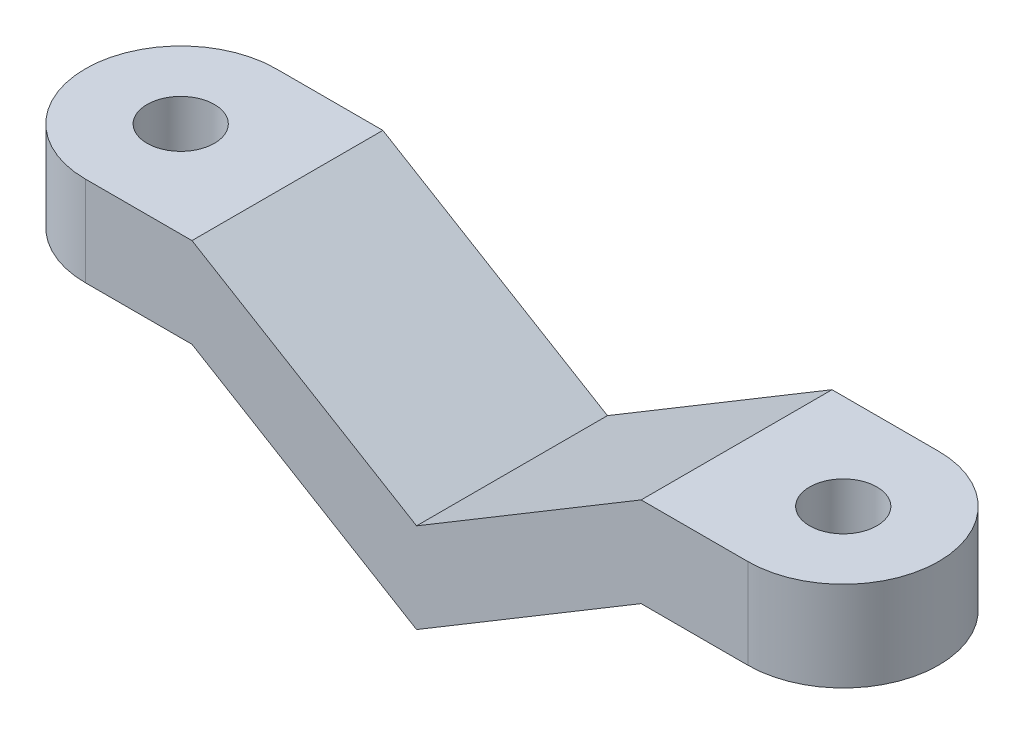
SolidWorks part; units mm, degrees
ref_plane "Front Plane" through (0, 0, 0) normal (0, 0, 1) x (1, 0, 0)
ref_plane "Top Plane" through (0, 0, 0) normal (0, 1, 0) x (1, 0, 0)
ref_plane "Right Plane" through (0, 0, 0) normal (1, 0, 0) x (0, 0, -1)
sketch "Sketch2" plane through (0, 0, 0) normal (0, 1, 0) x (1, 0, 0)
  line L0 (0, -4.25) -> (29.5, -4.25)
  line L1 (0, 4.25) -> (29.5, 4.25)
  arc A0 (0, -4.25) -> (0, 4.25) centre (0, 0) cw
  arc A1 (29.5, 4.25) -> (29.5, -4.25) centre (29.5, 0) cw
  dimension "D2" = 4.25
  dimension "D1" = 29.5
extrude "Boss-Extrude1" add sketch "Sketch2" along normal blind 10 contours L1 A1 L0 A0
sketch "Sketch3" plane through (0, 0, 4.25) normal (0, 0, 1) x (1, 0, 0)
  line L0 (4.75, 10) -> (14.75, 4)
  line L1 (0, 10) -> (29.5, 10) construction
  line L2 (14.75, 4) -> (24.75, 10)
  line L3 (24.75, 10) -> (4.75, 10)
  line L4 (-4.25, 6) -> (4.75, 6)
  line L5 (-4.25, 10) -> (-4.25, 0) construction
  line L6 (4.75, 6) -> (14.75, 0)
  line L7 (14.75, 0) -> (24.75, 6)
  line L8 (24.75, 6) -> (33.75, 6)
  line L9 (33.75, 0) -> (33.75, 10) construction
  line L10 (-4.25, 0) -> (-4.25, 6)
  line L12 (-4.25, 0) -> (33.75, 0)
  line L13 (33.75, 0) -> (33.75, 6)
  line L14 (0, 0) -> (29.5, 0) construction
  line M9 (0, 0) -> (29.5, 0)
  line M10 (29.5, 0) -> (29.5, 10)
  line M11 (29.5, 10) -> (0, 10)
  line M12 (0, 10) -> (0, 0)
  dimension "D1" = 9
  dimension "D2" = 9
  dimension "D4" = 4
extrude "Cut-Extrude1" cut sketch "Sketch3" against normal blind 10 contours L0 L2 M11 | L6 L4 M12 M9 | L10 L12 L4 M12 | L8 L7 M9 M10 | L12 L13 L8 M10
sketch "Sketch4" plane through (0, 10, 0) normal (0, 1, 0) x (1, 0, 0)
  circle A0 centre (0, 0) radius 1.5
  circle A1 centre (29.5, 0) radius 1.5
  arc A2 (29.5, -4.25) -> (29.5, 4.25) centre (29.5, 0) ccw construction
  arc A3 (0, 4.25) -> (0, -4.25) centre (0, 0) ccw construction
  dimension "D1" = 3
  dimension "D2" = 3
extrude "Cut-Extrude2" cut sketch "Sketch4" against normal through all
